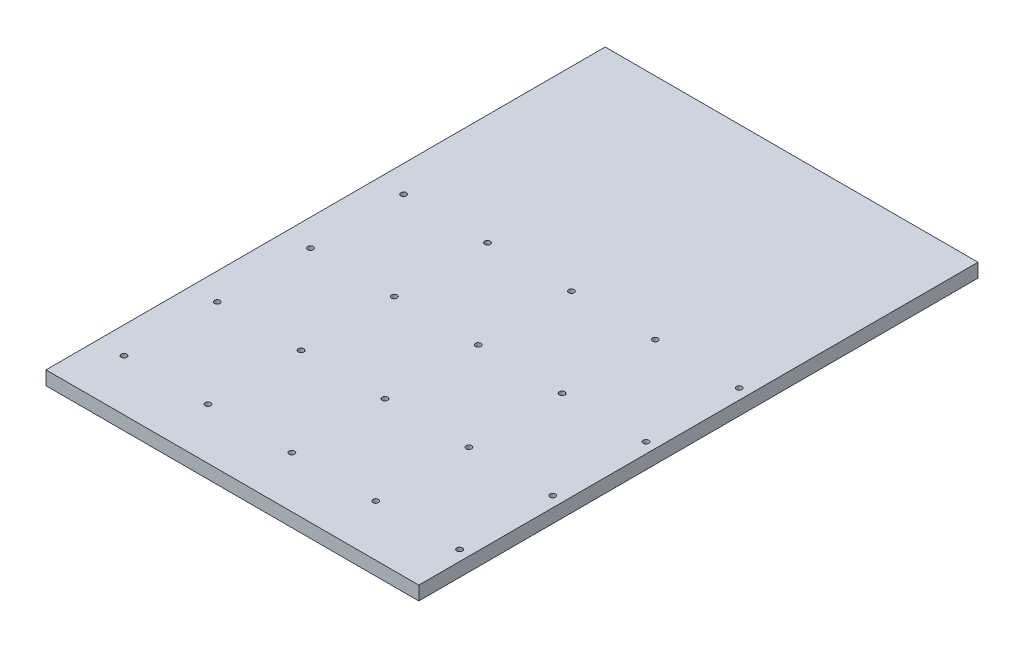
SolidWorks part; units mm, degrees
ref_plane "Front Plane" through (0, 0, 0) normal (0, 0, 1) x (1, 0, 0)
ref_plane "Top Plane" through (0, 0, 0) normal (0, 1, 0) x (1, 0, 0)
ref_plane "Right Plane" through (0, 0, 0) normal (1, 0, 0) x (0, 0, -1)
sketch "Sketch1" plane through (0, 0, 0) normal (0, 1, 0) x (1, 0, 0)
  line L0 (28.75, 355) -> (118.75, 355) construction
  line L1 (0, 0) -> (400, 0)
  line L2 (0, 0) -> (0, 600)
  line L3 (0, 600) -> (400, 600)
  line L4 (400, 0) -> (400, 600)
  line L5 (0, 0) -> (400, 600) construction
  line L6 (0, 600) -> (400, 0) construction
  line L7 (118.75, 355) -> (208.75, 355) construction
  line L8 (208.75, 355) -> (298.75, 355) construction
  line L9 (298.75, 355) -> (388.75, 355) construction
  circle A0 centre (28.75, 355) radius 3
  circle A1 centre (118.75, 355) radius 3
  circle A2 centre (208.75, 355) radius 3
  circle A3 centre (298.75, 355) radius 3
  circle A4 centre (388.75, 355) radius 3
  circle A5 centre (28.75, 255) radius 3
  circle A6 centre (118.75, 255) radius 3
  circle A7 centre (208.75, 255) radius 3
  circle A8 centre (298.75, 255) radius 3
  circle A9 centre (388.75, 255) radius 3
  circle A10 centre (28.75, 155) radius 3
  circle A11 centre (118.75, 155) radius 3
  circle A12 centre (208.75, 155) radius 3
  circle A13 centre (298.75, 155) radius 3
  circle A14 centre (388.75, 155) radius 3
  circle A15 centre (28.75, 55) radius 3
  circle A16 centre (118.75, 55) radius 3
  circle A17 centre (208.75, 55) radius 3
  circle A18 centre (298.75, 55) radius 3
  circle A19 centre (388.75, 55) radius 3
  point P4 (200, 300)
  point P17 (200, 338.0837)
  point P47 (0, 0)
  dimension "D3" = 6
  dimension "D1" = 600
  dimension "D2" = 400
  dimension "D4" = 90
  dimension "D6" = 55
  dimension "D7" = 100
  dimension "D8" = 28.75
  dimension "D5" = 4
extrude "Boss-Extrude1" add sketch "Sketch1" along normal blind 14.8
